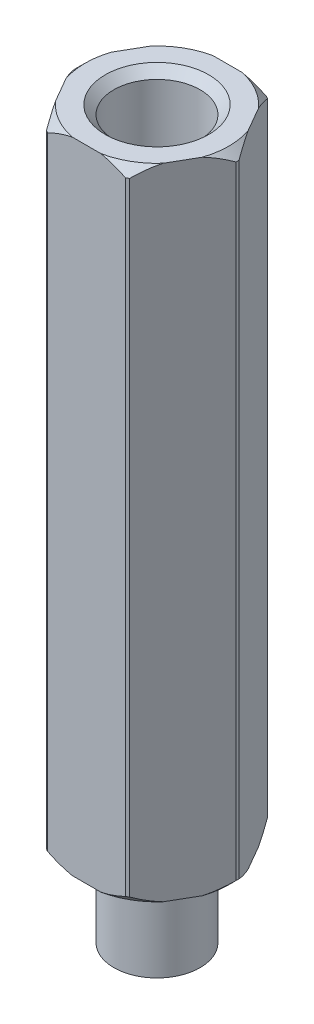
SolidWorks part; units mm, degrees
ref_plane "Front Plane" through (0, 0, 0) normal (0, 0, 1) x (1, 0, 0)
ref_plane "Top Plane" through (0, 0, 0) normal (0, 1, 0) x (1, 0, 0)
ref_plane "Right Plane" through (0, 0, 0) normal (1, 0, 0) x (0, 0, -1)
sketch "Sketch2" plane through (0, 0, 0) normal (0, 0, 1) x (1, 0, 0)
  line L0 (0, 0) -> (-1.5, 0)
  line L1 (-1.5, 0) -> (-1.5, 3)
  line L2 (-1.5, 3) -> (-2.8, 3)
  line L3 (-2.8, 3) -> (-2.8, 25.24)
  line L4 (-2.8, 25.24) -> (0, 25.24)
  line L5 (0, 0) -> (0, 25.24)
  line L7 (0, 33.3982) -> (0, -9.9228) construction
  dimension "D1" = 3
  dimension "D2" = 5.6
revolve "Revolve3" add sketch "Sketch2" angle 360 about L7
sketch "Sketch3" plane through (0, 25.24, 0) normal (0, 1, 0) x (1, 0, 0)
  circle A0 centre (0, 0) radius 1.5
  dimension "D1" = 3
extrude "Extrude1" cut sketch "Sketch3" against normal blind 12
chamfer "Chamfer1" distance 0.3 angle 45 3 edges at (0, 3, 2.8) (0, 25.24, 2.8) (0, 25.24, 1.5)
sketch "Sketch4" plane through (0, 25.24, 0) normal (0, 1, 0) x (1, 0, 0)
  line L1 (2.829, 0) -> (1.4145, 2.45)
  line L2 (1.4145, 2.45) -> (-1.4145, 2.45)
  line L3 (-1.4145, 2.45) -> (-2.829, 0)
  line L4 (-2.829, 0) -> (-1.4145, -2.45)
  line L5 (-1.4145, -2.45) -> (1.4145, -2.45)
  line L6 (1.4145, -2.45) -> (2.829, 0)
  circle A0 centre (0, 0) radius 2.45 construction
  dimension "D1" = 4.9
extrude "Extrude2" cut sketch "Sketch4" against normal through all flip side to cut
